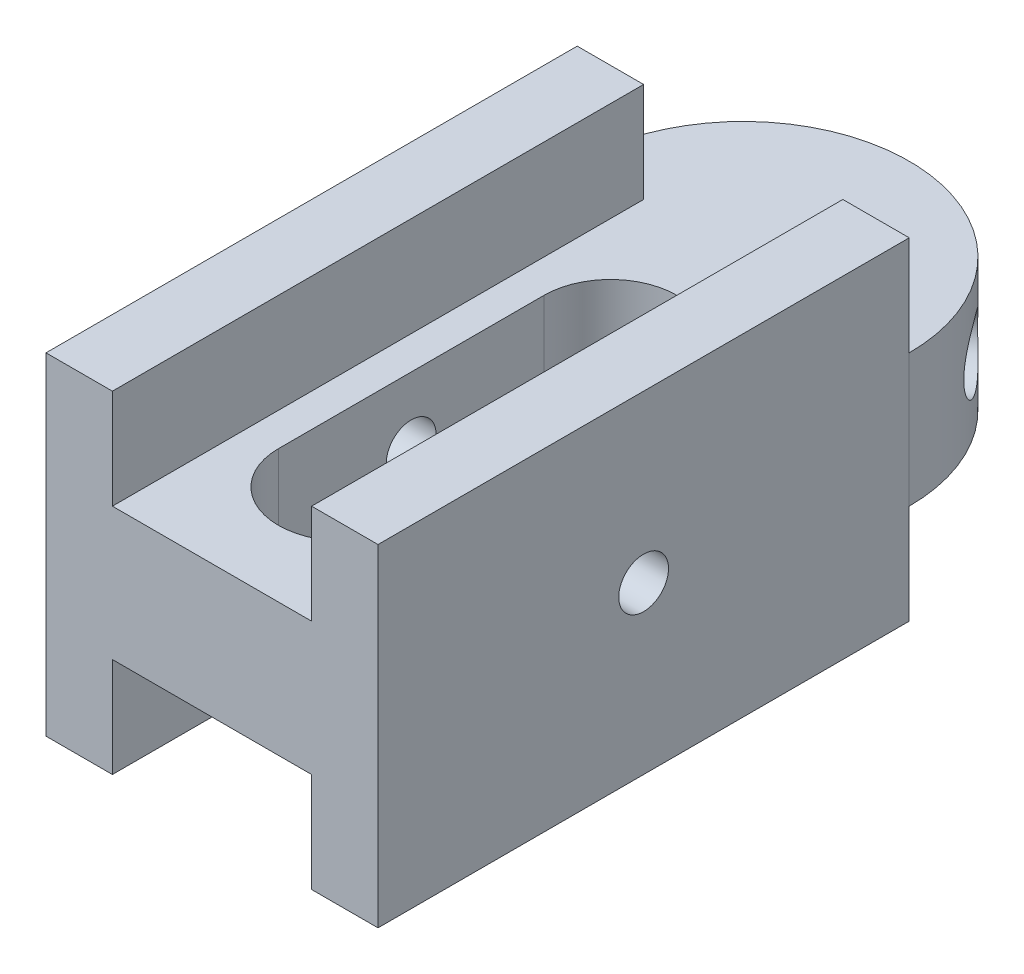
SolidWorks part; units mm, degrees
ref_plane "Front Plane" through (0, 0, 0) normal (0, 0, 1) x (1, 0, 0)
ref_plane "Top Plane" through (0, 0, 0) normal (0, 1, 0) x (1, 0, 0)
ref_plane "Right Plane" through (0, 0, 0) normal (1, 0, 0) x (0, 0, -1)
sketch "Sketch1" plane through (0, 0, 0) normal (0, 0, 1) x (1, 0, 0)
  line L1 (-9.525, 9.525) -> (9.525, 9.525) construction
  line L2 (-9.525, 9.525) -> (-9.525, -9.525) construction
  line L3 (-9.525, -9.525) -> (9.525, -9.525) construction
  line L4 (9.525, 9.525) -> (9.525, -9.525) construction
  line L5 (-9.525, 9.525) -> (9.525, -9.525) construction
  line L6 (-9.525, -9.525) -> (9.525, 9.525) construction
  line L7 (-7.9375, 7.9375) -> (7.9375, 7.9375)
  line L8 (-7.9375, 7.9375) -> (-7.9375, -7.9375)
  line L9 (-7.9375, -7.9375) -> (7.9375, -7.9375)
  line L10 (7.9375, 7.9375) -> (7.9375, -7.9375)
  line L11 (-7.9375, 7.9375) -> (7.9375, -7.9375) construction
  line L12 (-7.9375, -7.9375) -> (7.9375, 7.9375) construction
  point P0 (0, 0)
  point P6 (0, 0)
  dimension "D1" = 19.05
  dimension "D2" = 19.05
  dimension "D3" = 1.5875
extrude "Boss-Extrude1" add sketch "Sketch1" along normal blind 25.4
ref_plane "Plane1" through (0, 0, 0) normal (0, 1, 0) x (1, 0, 0)
sketch "Sketch3" plane through (0, 0, 0) normal (0, 1, 0) x (1, 0, 0)
  line L0 (7.9375, 0) -> (-7.9375, 0) construction
  line L1 (-7.9375, 0) -> (7.9375, 0)
  arc A0 (-7.9375, 0) -> (7.9375, 0) centre (0, 0) cw
extrude "Boss-Extrude3" add sketch "Sketch3" along normal blind 3.175 and the other way blind 3.175
sketch "Sketch4" plane through (7.9375, 0, 0) normal (1, 0, 0) x (0, 0, -1)
  line L0 (-25.4, 0) -> (0, 0) construction
  line L1 (-25.4, -7.9375) -> (-25.4, 7.9375) construction
  line L2 (-12.7, 7.9375) -> (-12.7, -7.9375) construction
  line L3 (-25.4, 7.9375) -> (0, 7.9375) construction
  line L4 (-25.4, -7.9375) -> (0, -7.9375) construction
  line L5 (-25.4, 0) -> (0, 0) construction
  circle A0 centre (-12.7, 0) radius 1.1906
  dimension "D1" = 2.3813
extrude "Cut-Extrude1" cut sketch "Sketch4" against normal through all
sketch "Sketch5" plane through (0, 0, 0) normal (0, 1, 0) x (1, 0, 0)
  line L0 (0, 0) -> (-4.7214, 6.3806)
  line L1 (0, 0) -> (6.3806, 4.7214)
  line L2 (-7.9375, 0) -> (7.9375, 0) construction
  arc A0 (7.9375, 0) -> (-7.9375, 0) centre (0, 0) ccw construction
  dimension "D1" = 53.5
ref_plane "Plane2" through (-4.7214, 0, -6.3806) normal (0.5948, 0, 0.8039) x (0.8039, 0, -0.5948)
sketch "Sketch7" plane through (-4.7214, 0, -6.3806) normal (0.5948, 0, 0.8039) x (0.8039, 0, -0.5948)
  circle A0 centre (0, 0) radius 1.5875
  dimension "D1" = 3.175
ref_plane "Plane3" through (6.3806, 0, -4.7214) normal (0.8039, 0, -0.5948) x (-0.5948, 0, -0.8039)
sketch "Sketch8" plane through (6.3806, 0, -4.7214) normal (0.8039, 0, -0.5948) x (-0.5948, 0, -0.8039)
  circle A0 centre (0, 0) radius 1.5875
  dimension "D1" = 3.175
extrude "Cut-Extrude3" cut sketch "Sketch8" against normal up to vertex (7.9375 mm away) contours A0 up to point (0, 0, 0)
extrude "Cut-Extrude4" cut sketch "Sketch7" along normal up to vertex (7.9375 mm away) contours A0 up to point (0, 0, 0)
sketch "Sketch9" plane through (0, 0, 0) normal (0, 0, -1) x (-1, 0, 0)
  line L0 (-7.9375, 7.9375) -> (7.9375, 7.9375) construction
  line L1 (-4.7625, 7.9375) -> (4.7625, 7.9375)
  line L2 (-4.7625, 7.9375) -> (-4.7625, 3.175)
  line L3 (-4.7625, 3.175) -> (4.7625, 3.175)
  line L4 (4.7625, 7.9375) -> (4.7625, 3.175)
  line L5 (7.9375, 3.175) -> (-7.9375, 3.175) construction
  line L6 (-7.9375, 3.175) -> (-7.9375, 7.9375) construction
  line L7 (7.9375, 7.9375) -> (7.9375, 3.175) construction
  line L8 (-7.9375, 0) -> (7.9375, 0) construction
  line L9 (-7.9375, -3.175) -> (-7.9375, 3.175) construction
  line L10 (7.9375, -3.175) -> (7.9375, 3.175) construction
  line L11 (-4.7625, -7.9375) -> (4.7625, -7.9375)
  line L12 (-4.7625, -3.175) -> (4.7625, -3.175)
  line L13 (4.7625, -7.9375) -> (4.7625, -3.175)
  line L14 (-4.7625, -7.9375) -> (-4.7625, -3.175)
  dimension "D1" = 3.175
  dimension "D2" = 3.175
extrude "Cut-Extrude5" cut sketch "Sketch9" against normal through all
sketch "Sketch10" plane through (0, -3.175, 0) normal (0, -1, 0) x (-1, 0, 0)
  line L0 (0, -25.4) -> (0, 0) construction
  line L1 (4.7625, -25.4) -> (-4.7625, -25.4) construction
  line L2 (0, -19.05) -> (0, -6.35) construction
  line L3 (-3.175, -19.05) -> (-3.175, -6.35)
  line L4 (3.175, -19.05) -> (3.175, -6.35)
  arc A0 (-3.175, -19.05) -> (3.175, -19.05) centre (0, -19.05) ccw
  arc A1 (3.175, -6.35) -> (-3.175, -6.35) centre (0, -6.35) ccw
  point P7 (0, -12.7)
  point P12 (0, -12.7)
  dimension "D1" = 6.35
  dimension "D2" = 12.7
extrude "Cut-Extrude6" cut sketch "Sketch10" against normal through all
